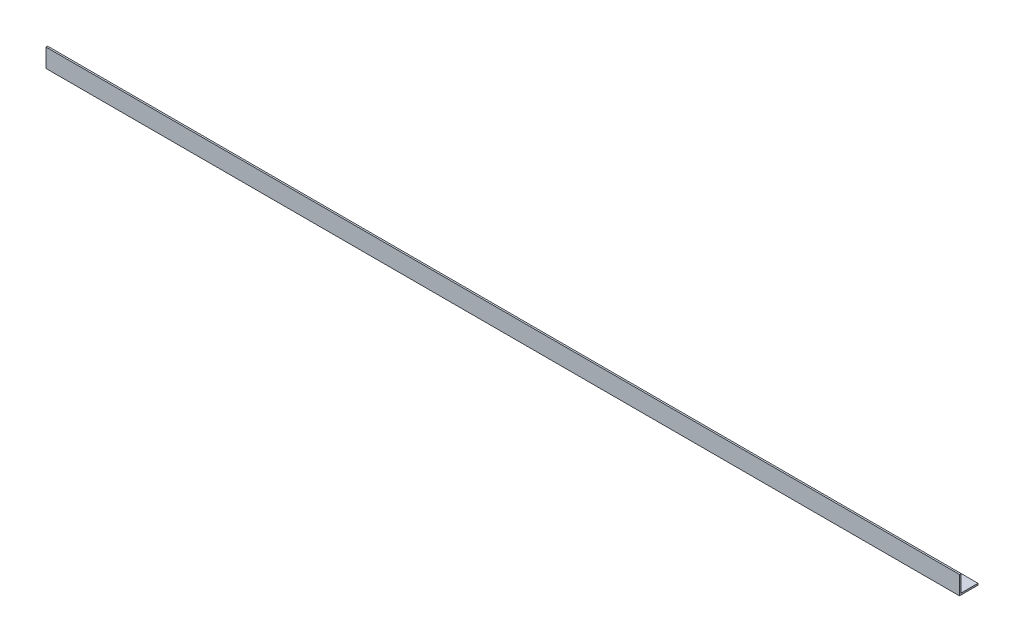
SolidWorks part; units mm, degrees
ref_plane "Спереди" through (0, 0, 0) normal (0, 0, 1) x (1, 0, 0)
ref_plane "Сверху" through (0, 0, 0) normal (0, 1, 0) x (1, 0, 0)
ref_plane "Справа" through (0, 0, 0) normal (1, 0, 0) x (0, 0, -1)
sketch "Эскиз1" plane through (0, 0, 0) normal (1, 0, 0) x (0, 0, -1)
  line L0 (0, 33.7) -> (0, 0)
  line L1 (0, 0) -> (33.7, 0)
extrude "Вытянуть-Тонкостенный1" add sketch "Эскиз1" along normal blind 1660 thin thin type one direction reverse wall 3
